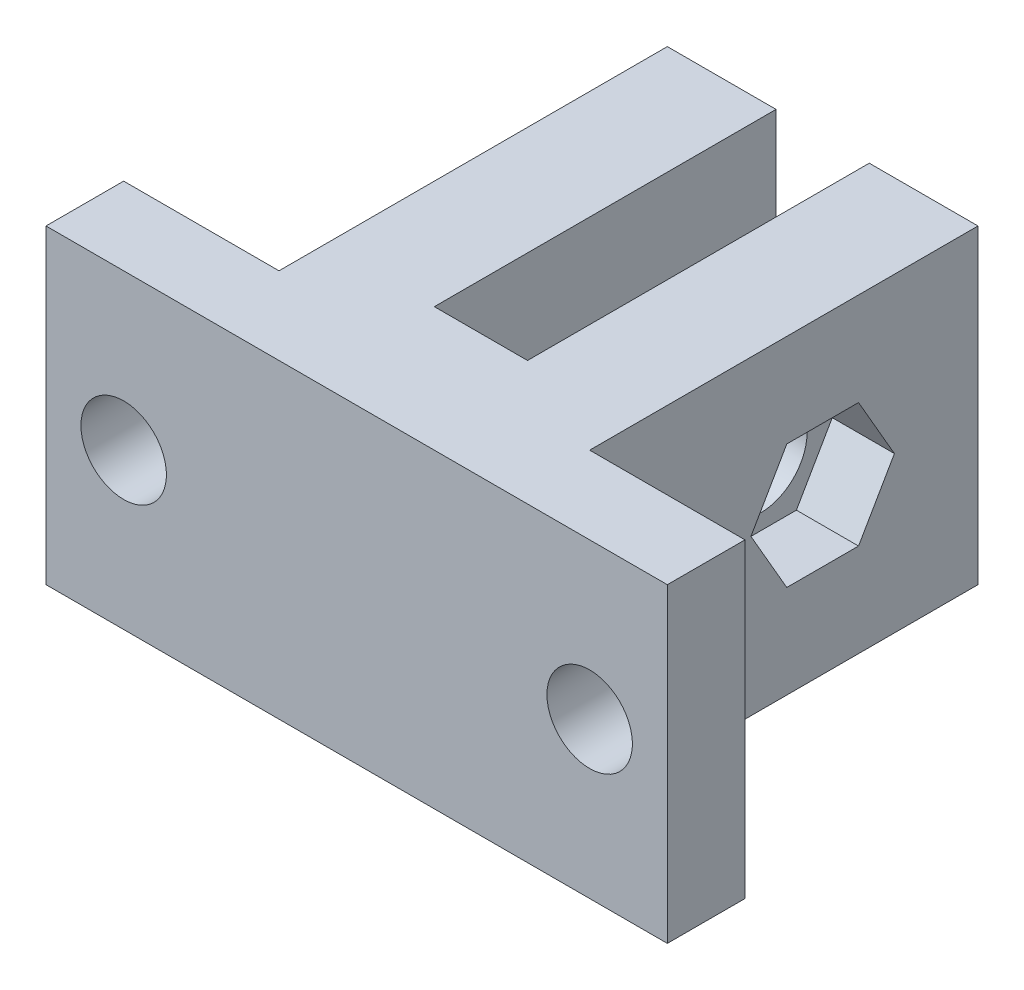
SolidWorks part; units mm, degrees
ref_plane "Front Plane" through (0, 0, 0) normal (0, 0, 1) x (1, 0, 0)
ref_plane "Top Plane" through (0, 0, 0) normal (0, 1, 0) x (1, 0, 0)
ref_plane "Right Plane" through (0, 0, 0) normal (1, 0, 0) x (0, 0, -1)
sketch "Sketch1" plane through (0, 0, 0) normal (0, 0, 1) x (1, 0, 0)
  line L1 (0, 0) -> (40, 0)
  line L2 (0, 0) -> (0, 20)
  line L3 (0, 20) -> (40, 20)
  line L4 (40, 0) -> (40, 20)
  dimension "D1" = 20
  dimension "D2" = 40
extrude "Boss-Extrude1" add sketch "Sketch1" along normal blind 30
sketch "Sketch2" plane through (0, 0, 0) normal (-1, 0, 0) x (0, 0, 1)
  line L0 (0, 20) -> (0, 0) construction
  line L1 (30, 0) -> (0, 0) construction
  circle A0 centre (10, 10) radius 3
  dimension "D1" = 6
  dimension "D2" = 10
  dimension "D3" = 10
extrude "Cut-Extrude1" cut sketch "Sketch2" against normal through all
sketch "Sketch3" plane through (0, 20, 0) normal (0, 1, 0) x (1, 0, 0)
  line L0 (40, 0) -> (0, 0) construction
  line L1 (23, 0) -> (17, 0)
  line L2 (23, 0) -> (23, -22)
  line L3 (23, -22) -> (17, -22)
  line L4 (17, 0) -> (17, -22)
  line L5 (40, -30) -> (40, 0) construction
  dimension "D1" = 22
  dimension "D2" = 6
  dimension "D3" = 17
extrude "Cut-Extrude2" cut sketch "Sketch3" against normal through all
sketch "Sketch4" plane through (0, 0, 0) normal (0, 0, -1) x (-1, 0, 0)
  line L1 (-40, 0) -> (-30, 0)
  line L2 (-40, 0) -> (-40, 20)
  line L3 (-40, 20) -> (-30, 20)
  line L4 (-30, 0) -> (-30, 20)
  line L5 (-40, 20) -> (-23, 20) construction
  line L6 (-17, 20) -> (0, 20) construction
  line L7 (0, 0) -> (-10, 0)
  line L8 (0, 0) -> (0, 20)
  line L9 (0, 20) -> (-10, 20)
  line L10 (-10, 0) -> (-10, 20)
  dimension "D1" = 20
  dimension "D2" = 10
  dimension "D3" = 10
extrude "Cut-Extrude3" cut sketch "Sketch4" against normal blind 25
sketch "Sketch5" plane through (0, 0, 25) normal (0, 0, -1) x (-1, 0, 0)
  line L0 (-30, 20) -> (-40, 20) construction
  line L1 (0, 20) -> (-10, 20) construction
  line L2 (0, 0) -> (0, 20) construction
  line L3 (-40, 20) -> (-40, 0) construction
  circle A0 centre (-35, 10) radius 2.75
  circle A1 centre (-5, 10) radius 2.75
  dimension "D1" = 5.5
  dimension "D2" = 5.5
  dimension "D3" = 10
  dimension "D4" = 10
  dimension "D5" = 5
  dimension "D6" = 5
extrude "Cut-Extrude4" cut sketch "Sketch5" against normal through all
sketch "Sketch6" plane through (30, 0, 0) normal (1, 0, 0) x (0, 0, -1)
  line L0 (-25, 20) -> (0, 20) construction
  line L1 (-7.6906, 14) -> (-12.3094, 14)
  line L2 (-12.3094, 14) -> (-14.6188, 10)
  line L3 (-14.6188, 10) -> (-12.3094, 6)
  line L4 (-12.3094, 6) -> (-7.6906, 6)
  line L5 (-7.6906, 6) -> (-5.3812, 10)
  line L6 (-5.3812, 10) -> (-7.6906, 14)
  circle A0 centre (-10, 10) radius 4 construction
  dimension "D1" = 8
extrude "Cut-Extrude5" cut sketch "Sketch6" against normal blind 4
